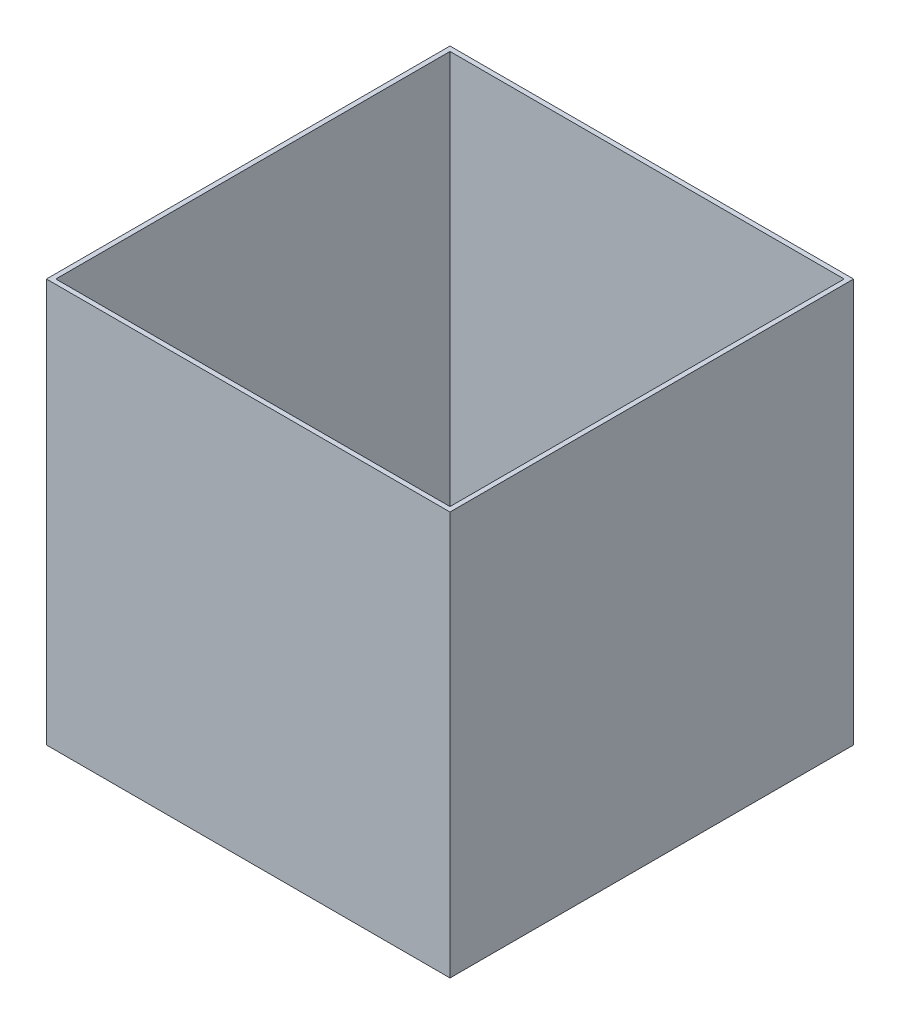
SolidWorks part; units mm, degrees
ref_plane "Front Plane" through (0, 0, 0) normal (0, 0, 1) x (1, 0, 0)
ref_plane "Top Plane" through (0, 0, 0) normal (0, 1, 0) x (1, 0, 0)
ref_plane "Right Plane" through (0, 0, 0) normal (1, 0, 0) x (0, 0, -1)
sketch "Sketch1" plane through (0, 0, 0) normal (0, 1, 0) x (1, 0, 0)
  line L1 (30, -30) -> (-30, -30)
  line L2 (30, -30) -> (30, 30)
  line L3 (30, 30) -> (-30, 30)
  line L4 (-30, -30) -> (-30, 30)
  line L5 (30, -30) -> (-30, 30) construction
  line L6 (30, 30) -> (-30, -30) construction
  point P0 (0, 0)
  dimension "D1" = 60
  dimension "D2" = 60
extrude "Boss-Extrude1" add sketch "Sketch1" along normal blind 60
shell "Shell1" thickness 0.7
